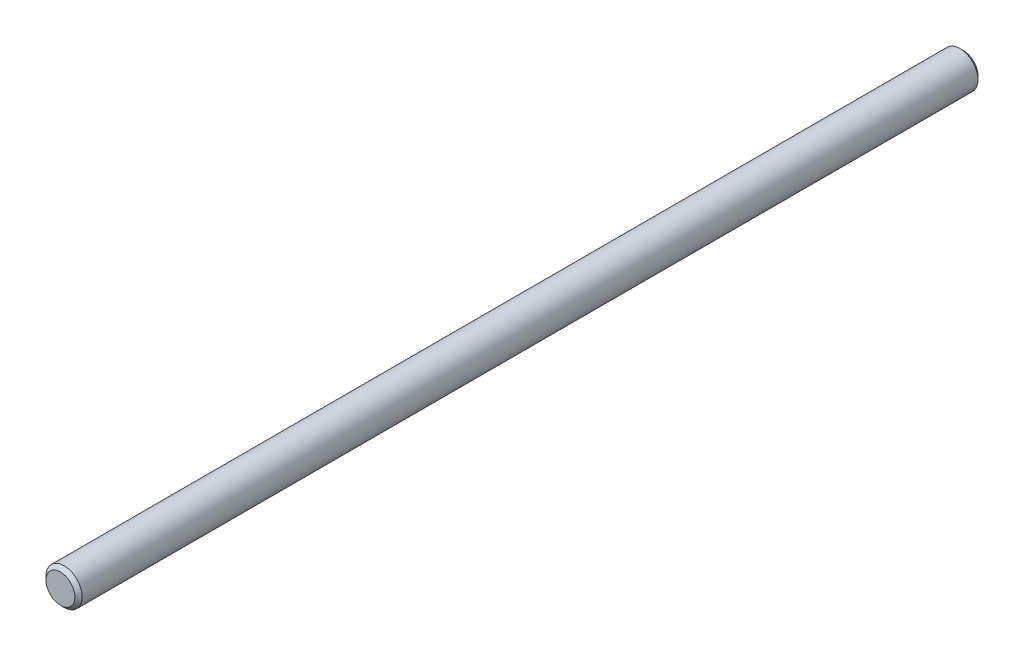
SolidWorks part; units mm, degrees
ref_plane "Front" through (0, 0, 0) normal (0, 0, 1) x (1, 0, 0)
ref_plane "Top" through (0, 0, 0) normal (0, 1, 0) x (1, 0, 0)
ref_plane "Right" through (0, 0, 0) normal (1, 0, 0) x (0, 0, -1)
sketch "Sketch1" plane through (0, 0, 0) normal (0, 0, 1) x (1, 0, 0)
  circle A0 centre (0, 0) radius 5
  dimension "D1" = 10
extrude "Extrude1" add sketch "Sketch1" along normal mid plane 250
chamfer "Chamfer1" distance 1 angle 45 2 edges at (5, 0, -125) (5, 0, 125)
equation "\"D1@Chamfer1\" = \"D1@Sketch1\" * .1"
